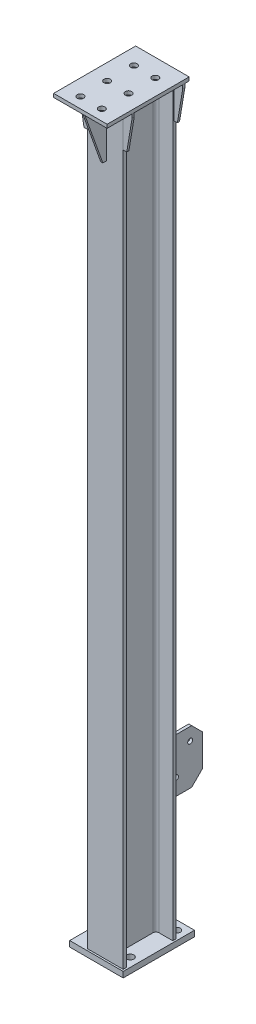
SolidWorks part; units mm, degrees
material "普通碳钢"
ref_plane "前视基准面" through (0, 0, 0) normal (0, 0, 1) x (1, 0, 0)
ref_plane "上视基准面" through (0, 0, 0) normal (0, 1, 0) x (1, 0, 0)
ref_plane "右视基准面" through (0, 0, 0) normal (1, 0, 0) x (0, 0, -1)
sketch "草图1" plane through (0, 0, 0) normal (1, 0, 0) x (0, 0, -1)
  line L0 (-7207.6682, -1518.1927) -> (-7207.6682, -3608.1927)
  dimension "D1" = 2090
other "H型钢 HM150×100(1)"
ref_plane "基准面4" through (-50, -1518.1927, 7133.6682) normal (0, -1, 0) x (1, 0, 0)
sketch "草图11" plane through (-50, -1518.1927, 7133.6682) normal (0, -1, 0) x (1, 0, 0)
  line L0 (-50, -74) -> (50, -74)
  line L1 (50, -74) -> (50, -65)
  line L2 (50, -65) -> (11, -65)
  line L3 (3, -57) -> (3, 57)
  line L4 (11, 65) -> (50, 65)
  line L5 (50, 65) -> (50, 74)
  line L6 (50, 74) -> (-50, 74)
  line L7 (0, 74) -> (0, -74) construction
  line L11 (0, 60) -> (0, 74) construction
  line L14 (-50, -74) -> (-50, -65)
  line L15 (-50, -65) -> (-11, -65)
  line L16 (-3, -57) -> (-3, 57)
  line L17 (-11, 65) -> (-50, 65)
  line L18 (-50, 65) -> (-50, 74)
  arc A2 (11, -65) -> (3, -57) centre (11, -57) cw
  arc A3 (3, 57) -> (11, 65) centre (11, 57) cw
  arc A5 (-11, -65) -> (-3, -57) centre (-11, -57) ccw
  arc A6 (-3, 57) -> (-11, 65) centre (-11, 57) ccw
  point P2 (0, 0)
  point P38 (0, 0)
  point P39 (50, 74)
  point P40 (50, -74)
  point P41 (-50, -74)
  dimension "D8" = 8
  dimension "D1" = 6
  dimension "D2" = 9
  dimension "D3" = 148
  dimension "D4" = 100
  dimension "D9" = 0
sketch "草图12" plane through (0, -3608.1927, 0) normal (0, -1, 0) x (1, 0, 0)
  line L0 (0, 7198.6682) -> (0, 7207.6682) construction
  line L1 (-145, 7212.6682) -> (5, 7212.6682)
  line L2 (-145, 7212.6682) -> (-145, 7012.6682)
  line L3 (-145, 7012.6682) -> (5, 7012.6682)
  line L4 (5, 7212.6682) -> (5, 7012.6682)
  line L5 (0, 7207.6682) -> (-100, 7207.6682) construction
  dimension "D1" = 5
  dimension "D2" = 5
  dimension "D3" = 200
  dimension "D4" = 150
extrude "凸台-拉伸1" add sketch "草图12" along normal blind 16 separate body contours L1 L4 L3 L2
sketch "草图13" plane through (-1618.1927, -1518.1927, 0) normal (0, -1, 0) x (0, 0, 1)
  line L1 (7047.6682, -1493.1927) -> (7277.6682, -1493.1927)
  line L2 (7047.6682, -1493.1927) -> (7047.6682, -1643.1927)
  line L3 (7047.6682, -1643.1927) -> (7277.6682, -1643.1927)
  line L4 (7277.6682, -1493.1927) -> (7277.6682, -1643.1927)
  line L5 (7059.6682, -1518.1927) -> (7059.6682, -1618.1927) construction
  line L6 (7207.6682, -1518.1927) -> (7198.6682, -1518.1927) construction
  line L7 (7198.6682, -1618.1927) -> (7207.6682, -1618.1927) construction
  dimension "D1" = 25
  dimension "D2" = 230
  dimension "D3" = 25
  dimension "D4" = 12
extrude "凸台-拉伸2" add sketch "草图13" against normal blind 10 separate body
sketch "草图15" plane through (1383.1927, -1508.1927, 0) normal (0, 1, 0) x (1, 0, 0)
  line L0 (-1433.1927, -7277.6682) -> (-1433.1927, -7007.6682) construction
  line L3 (-1463.1927, -7207.6682) -> (-1463.1927, -7007.6682) construction
  line L4 (-1403.1927, -7207.6682) -> (-1403.1927, -7007.6682) construction
  line L5 (-1508.1927, -7247.6682) -> (-691.4022, -7247.6682) construction
  line L6 (-1358.1927, -7277.6682) -> (-1508.1927, -7277.6682) construction
  line L8 (-1508.1927, -7277.6682) -> (-1508.1927, -7047.6682) construction
  line L9 (-1508.1927, -7172.6682) -> (4217.5291, -7172.6682) construction
  line L10 (-1508.1927, -7097.6682) -> (-596.147, -7097.6682) construction
  circle A0 centre (-1403.1927, -7247.6682) radius 9
  circle A1 centre (-1463.1927, -7247.6682) radius 9
  circle A2 centre (-1463.1927, -7172.6682) radius 9
  circle A3 centre (-1403.1927, -7172.6682) radius 9
  circle A4 centre (-1403.1927, -7097.6682) radius 9
  circle A5 centre (-1463.1927, -7097.6682) radius 9
  dimension "D6" = 18
  dimension "D1" = 30
  dimension "D2" = 75
  dimension "D3" = 75
  dimension "D4" = 30
  dimension "D5" = 30
extrude "切除-拉伸2" cut sketch "草图15" against normal up to next (10 mm away)
sketch "草图16" plane through (0, 0, 7207.6682) normal (0, 0, 1) x (1, 0, 0)
  line L0 (-125, -1518.1927) -> (-125, -1528.1927)
  line L1 (-125, -1528.1927) -> (-110, -1618.1927)
  line L2 (-110, -1618.1927) -> (-100, -1618.1927)
  line L3 (-100, -3608.1927) -> (-100, -1518.1927) construction
  line L4 (-100, -1618.1927) -> (-100, -1518.1927)
  line L5 (-100, -1518.1927) -> (-125, -1518.1927)
  line L6 (25, -1518.1927) -> (0, -1518.1927)
  line L7 (0, -1518.1927) -> (0, -1618.1927)
  line L8 (0, -1518.1927) -> (0, -3608.1927) construction
  line L9 (0, -1618.1927) -> (10, -1618.1927)
  line L10 (10, -1618.1927) -> (25, -1528.1927)
  line L11 (25, -1528.1927) -> (25, -1518.1927)
  line L12 (25, -1508.1927) -> (25, -1518.1927) construction
  dimension "D1" = 10
  dimension "D2" = 10
  dimension "D3" = 10
  dimension "D4" = 10
  dimension "D5" = 100
  dimension "D6" = 100
extrude "凸台-拉伸3" add sketch "草图16" against normal blind 6 separate body
sketch "草图17" plane through (0, 0, 7059.6682) normal (0, 0, -1) x (-1, 0, 0)
  line L5 (-25, -1518.1927) -> (-25, -1528.1927)
  line L6 (-25, -1528.1927) -> (-10, -1618.1927)
  line L7 (-10, -1618.1927) -> (0, -1618.1927)
  line L8 (0, -1618.1927) -> (0, -1518.1927)
  line L9 (0, -1518.1927) -> (-25, -1518.1927)
  line L10 (-25, -1518.1927) -> (-25, -1528.1927)
  line L11 (-25, -1528.1927) -> (-10, -1618.1927)
  line L12 (-10, -1618.1927) -> (0, -1618.1927)
  line L13 (0, -1618.1927) -> (0, -1518.1927)
  line L14 (0, -1518.1927) -> (-25, -1518.1927)
  line L15 (125, -1518.1927) -> (100, -1518.1927)
  line L16 (100, -1518.1927) -> (100, -1618.1927)
  line L17 (100, -1618.1927) -> (110, -1618.1927)
  line L18 (110, -1618.1927) -> (125, -1528.1927)
  line L19 (125, -1528.1927) -> (125, -1518.1927)
  line L20 (125, -1518.1927) -> (100, -1518.1927)
  line L21 (100, -1518.1927) -> (100, -1618.1927)
  line L22 (100, -1618.1927) -> (110, -1618.1927)
  line L23 (110, -1618.1927) -> (125, -1528.1927)
  line L24 (125, -1528.1927) -> (125, -1518.1927)
  dimension "D1" = 0
  dimension "D2" = 0
extrude "凸台-拉伸4" add sketch "草图17" against normal blind 6 separate body
sketch "草图18" plane through (-47, 0, 0) normal (1, 0, 0) x (0, 0, -1)
  line L0 (-7207.6682, -1518.1927) -> (-7267.6682, -1518.1927)
  line L1 (-7267.6682, -1518.1927) -> (-7267.6682, -1528.1927)
  line L2 (-7267.6682, -1528.1927) -> (-7217.6682, -1668.1927)
  line L3 (-7217.6682, -1668.1927) -> (-7207.6682, -1668.1927)
  line L4 (-7207.6682, -1668.1927) -> (-7207.6682, -1518.1927)
  line L5 (-7207.6682, -1618.1927) -> (-7207.6682, -1528.1927) construction
  line L6 (-7047.6682, -1518.1927) -> (-7277.6682, -1518.1927) construction
  dimension "D1" = 10
  dimension "D2" = 10
  dimension "D3" = 60
  dimension "D4" = 150
extrude "凸台-拉伸5" add sketch "草图18" against normal up to surface (6 mm away) separate body up to face at (-53, -2563.1927, 7133.6682)
sketch "草图19" plane through (0, 0, 7059.6682) normal (0, 0, -1) x (-1, 0, 0)
  line L0 (0, -3608.1927) -> (0, -1518.1927) construction
  line L1 (46, -3158.1927) -> (54, -3158.1927)
  line L2 (46, -3158.1927) -> (46, -3308.1927)
  line L3 (46, -3308.1927) -> (54, -3308.1927)
  line L4 (54, -3158.1927) -> (54, -3308.1927)
  line L5 (100, -3608.1927) -> (0, -3608.1927) construction
  dimension "D1" = 46
  dimension "D2" = 8
  dimension "D3" = 150
  dimension "D4" = 300
extrude "凸台-拉伸6" add sketch "草图19" along normal blind 120 separate body
sketch "草图23" plane through (0, -3608.1927, 0) normal (0, 1, 0) x (1, 0, 0)
  line L0 (-120, -7037.6682) -> (-120, -7167.6682) construction
  line L1 (-120, -7167.6682) -> (-20, -7167.6682) construction
  line L2 (-20, -7167.6682) -> (-20, -7037.6682) construction
  line L3 (-20, -7037.6682) -> (-120, -7037.6682) construction
  line L4 (-145, -7012.6682) -> (5, -7012.6682) construction
  line L6 (-145, -7212.6682) -> (-145, -7012.6682) construction
  circle A0 centre (-120, -7037.6682) radius 10
  circle A1 centre (-120, -7167.6682) radius 10
  circle A2 centre (-20, -7037.6682) radius 10
  circle A3 centre (-20, -7167.6682) radius 10
  dimension "D1" = 25
  dimension "D5" = 20
  dimension "D2" = 25
  dimension "D3" = 100
  dimension "D4" = 130
extrude "切除-拉伸5" cut sketch "草图23" against normal up to next (16 mm away)
chamfer "倒角1" distance 30 angle 45 2 edges at (-50, -3308.1927, 6939.6682) (-50, -3158.1927, 6939.6682)
sketch "草图20" plane through (-46, 0, 0) normal (1, 0, 0) x (0, 0, -1)
  line L0 (-7039.6682, -3308.1927) -> (-6801.5708, -2895.796) construction
  line L1 (-6969.6682, -3308.1927) -> (-7059.6682, -3308.1927) construction
  line L2 (-7059.6682, -3158.1927) -> (-7059.6682, -3308.1927) construction
  line L5 (-6969.6682, -3263.1927) -> (-7059.6682, -3263.1927)
  line L6 (-6969.6682, -3263.1927) -> (-7059.6682, -3263.1927) construction
  circle A0 centre (-7013.6874, -3263.1927) radius 7
  circle A1 centre (-6973.6874, -3193.9106) radius 7
  dimension "D4" = 14
  dimension "D5" = 14
  dimension "D1" = 60
  dimension "D2" = 20
  dimension "D6" = 80
  dimension "D3" = 45
extrude "切除-拉伸3" cut sketch "草图20" against normal blind 120
